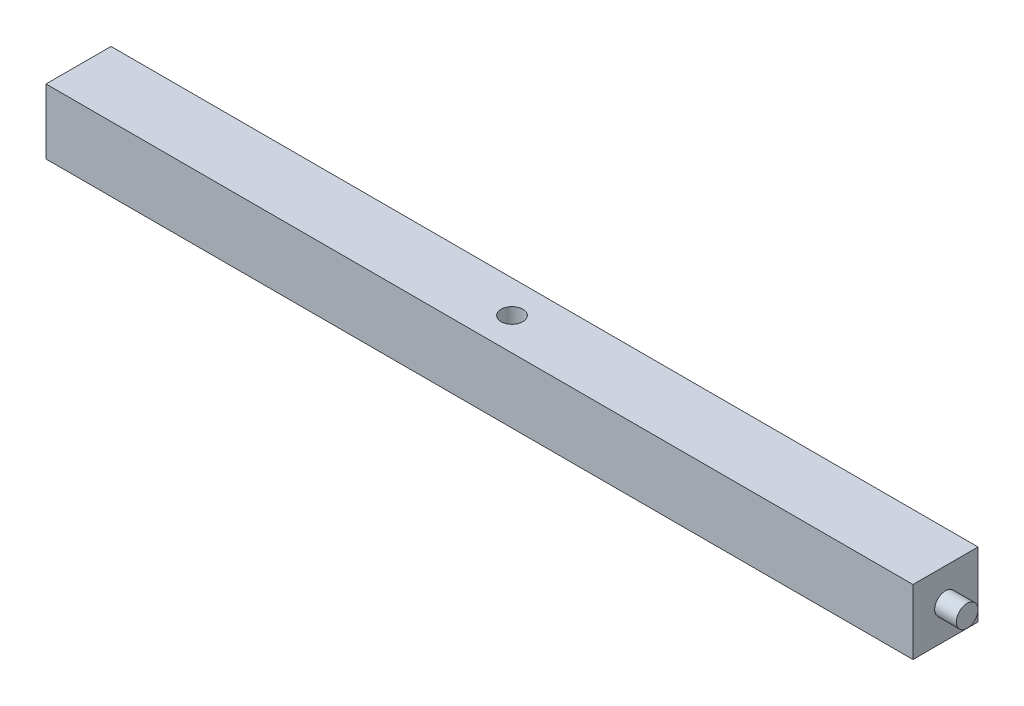
SolidWorks part; units mm, degrees
ref_plane "Alzado" through (0, 0, 0) normal (0, 0, 1) x (1, 0, 0)
ref_plane "Planta" through (0, 0, 0) normal (0, 1, 0) x (1, 0, 0)
ref_plane "Vista lateral" through (0, 0, 0) normal (1, 0, 0) x (0, 0, -1)
sketch "Croquis1" plane through (0, 0, 0) normal (0, 1, 0) x (1, 0, 0)
  line L1 (-254, 19.05) -> (254, 19.05)
  line L2 (-254, 19.05) -> (-254, -19.05)
  line L3 (-254, -19.05) -> (254, -19.05)
  line L4 (254, 19.05) -> (254, -19.05)
  line L5 (-254, 19.05) -> (254, -19.05) construction
  line L6 (-254, -19.05) -> (254, 19.05) construction
  point P1 (0, 0)
  dimension "D1" = 508
  dimension "D2" = 38.1
extrude "Saliente-Extruir1" add sketch "Croquis1" along normal blind 38.1
sketch "Croquis2" plane through (-254, 0, 0) normal (-1, 0, 0) x (0, 0, 1)
  line L0 (0, 0) -> (0, 38.1) construction
  line L1 (-19.05, 38.1) -> (19.05, 38.1) construction
  line L2 (-19.05, 19.05) -> (19.05, 19.05) construction
  line L3 (-19.05, 38.1) -> (-19.05, 0) construction
  line L4 (19.05, 38.1) -> (19.05, 0) construction
  circle A0 centre (0, 19.05) radius 6.35
  dimension "D1" = 12.7
extrude "Saliente-Extruir2" add sketch "Croquis2" along normal blind 12.7
sketch "Croquis3" plane through (254, 0, 0) normal (1, 0, 0) x (0, 0, -1)
  line L0 (0, 0) -> (0, 38.1) construction
  line L1 (-19.05, 38.1) -> (19.05, 38.1) construction
  line L2 (-19.05, 19.05) -> (19.05, 19.05) construction
  line L3 (-19.05, 38.1) -> (-19.05, 0) construction
  line L4 (19.05, 38.1) -> (19.05, 0) construction
  circle A0 centre (0, 19.05) radius 6.35
  dimension "D1" = 12.7
extrude "Saliente-Extruir3" add sketch "Croquis3" along normal blind 12.7
sketch "Croquis4" plane through (0, 38.1, 0) normal (0, 1, 0) x (1, 0, 0)
  circle A0 centre (0, 0) radius 6.35
  dimension "D1" = 12.7
extrude "Cortar-Extruir1" cut sketch "Croquis4" against normal blind 12.7
